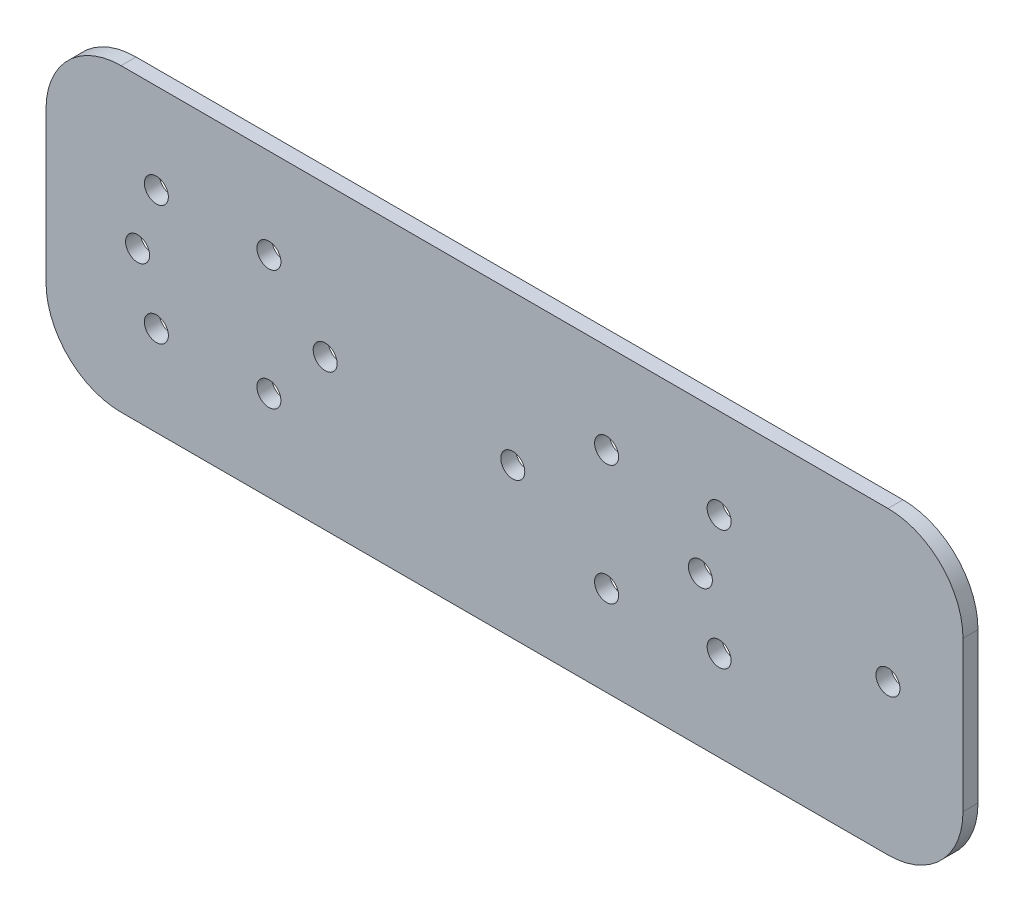
SolidWorks part; units mm, degrees
material "A-玻璃纤维"
ref_plane "前视基准面" through (0, 0, 0) normal (0, 0, 1) x (1, 0, 0)
ref_plane "上视基准面" through (0, 0, 0) normal (0, 1, 0) x (1, 0, 0)
ref_plane "右视基准面" through (0, 0, 0) normal (1, 0, 0) x (0, 0, -1)
sketch "草图1" plane through (0, 0, 0) normal (0, 0, 1) x (1, 0, 0)
  line L0 (-112.3648, 0) -> (117.0256, 0) construction
  line L1 (-70, -20) -> (70, -20)
  line L2 (-70, -20) -> (-70, 20)
  line L3 (-70, 20) -> (70, 20)
  line L4 (70, -20) -> (70, 20)
  line L5 (-70, -20) -> (70, 20) construction
  line L6 (-70, 20) -> (70, -20) construction
  line L7 (0, 38.0852) -> (0, -37.993) construction
  line L8 (30, 30.8138) -> (30, -35.4073) construction
  circle A9 centre (37.5, 8) radius 1.6
  circle A10 centre (37.5, -8) radius 1.6
  circle A11 centre (22.5, -8) radius 1.6
  circle A12 centre (22.5, 8) radius 1.6
  circle A13 centre (-22.5, -8) radius 1.6
  circle A14 centre (-37.5, -8) radius 1.6
  circle A15 centre (-22.5, 8) radius 1.6
  circle A16 centre (-37.5, 8) radius 1.6
  circle A17 centre (60, 0) radius 1.6
  circle A18 centre (35, 0) radius 1.6
  circle A19 centre (10, 0) radius 1.6
  circle A20 centre (-15, 0) radius 1.6
  circle A21 centre (-40, 0) radius 1.6
  circle A23 centre (-65, 0) radius 1.6 [skipped]
  point P0 (0, 0)
  dimension "D1" = 3.2
  dimension "D3" = 6
  dimension "D5" = 16
  dimension "D6" = 15
  dimension "D2" = 60
  dimension "D9" = 3.2
  dimension "D10" = 25
  dimension "D4" = 30
  dimension "D7" = 40
  dimension "D8" = 140
extrude "凸台-拉伸1" add sketch "草图1" along normal blind 2
fillet "圆角1" radius 10 4 edges at (70, -20, 1) (70, 20, 1) (-70, -20, 1) (-70, 20, 1)
sketch "草图2" plane through (0, 0, 2) normal (0, 0, 1) x (1, 0, 0)
  line L0 (-52.2068, 20) -> (-52.2068, -20)
  line L1 (60, 20) -> (-60, 20) construction
  line L2 (-60, -20) -> (60, -20) construction
  line L3 (-52.2068, -20) -> (-76.6461, -20)
  line L4 (-76.6461, -20) -> (-76.6461, 20)
  line L5 (-76.6461, 20) -> (-52.2068, 20)
  line L6 (70, -10) -> (70, 10) construction
  dimension "D1" = 122.2068
extrude "切除-拉伸1" cut sketch "草图2" against normal blind 10
fillet "圆角2" radius 10 2 edges at (-52.2068, 20, 1) (-52.2068, -20, 1)
